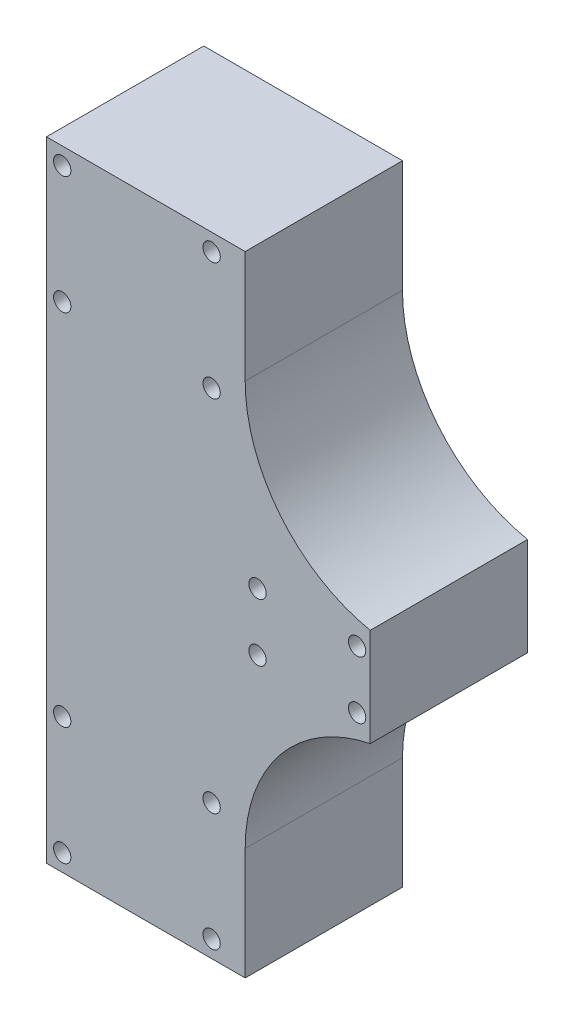
SolidWorks part; units mm, degrees
ref_plane "Front Plane" through (0, 0, 0) normal (0, 0, 1) x (1, 0, 0)
ref_plane "Top Plane" through (0, 0, 0) normal (0, 1, 0) x (1, 0, 0)
ref_plane "Right Plane" through (0, 0, 0) normal (1, 0, 0) x (0, 0, -1)
sketch "Sketch1" plane through (0, 0, 0) normal (0, 0, 1) x (1, 0, 0)
  line L0 (895.5, 2378.5486) -> (895.5, 2138.5486) construction
  line L2 (971.3, 2138.5486) -> (971.3, 2181.3478)
  line L3 (895, 2378.5486) -> (971.3, 2378.5486)
  line L4 (895, 2378.5486) -> (895, 2138.5486)
  line L5 (895, 2258.5486) -> (895.5, 2258.5486)
  line L6 (1019, 2277.2672) -> (1019, 2239.83)
  line L10 (971.3, 2378.5486) -> (971.3, 2335.7493)
  line L12 (895, 2138.5486) -> (971.3, 2138.5486)
  arc A0 (1019, 2277.2672) -> (971.3, 2335.7493) centre (1031.0008, 2335.7493) cw
  arc A1 (1019, 2239.83) -> (971.3, 2181.3478) centre (1031.0008, 2181.3478) ccw
extrude "Boss-Extrude1" add sketch "Sketch1" along normal blind 60
hole_wizard "M6 Clearance Hole1" positions "Sketch2" profile "Sketch3" hole size "M6" standard "ISO" end condition through all
sketch "Sketch2" plane through (0, 0, 60) normal (0, 0, 1) x (1, 0, 0)
  point P0 (901.5, 2145.0486)
  point P2 (958.5, 2145.0486)
  point P4 (958.5, 2190.0486)
  point P6 (901.5, 2190.0486)
  point P8 (901.5, 2372.0486)
  point P10 (901.5, 2327.0486)
  point P12 (958.5, 2327.0486)
  point P14 (958.5, 2372.0486)
  point P16 (1014, 2247.5486)
  point P18 (1014, 2269.5486)
  point P20 (976, 2247.5486)
  point P22 (976, 2269.5486)
sketch "Sketch3" plane through (901.5, 2145.0486, 60) normal (1, 0, 0) x (0, -1, 0)
  line L0 (0, 0) -> (0, 60)
  line L1 (0, 60) -> (3.3, 60)
  line L2 (3.3, 60) -> (3.3, 0)
  line L5 (3.3, 0) -> (0, 0)
  line L11 (0, -6.35) -> (0, 107.95) construction
  dimension "Thru Hole Dia." = 6.6
  dimension "Thru Hole Depth" = 60
